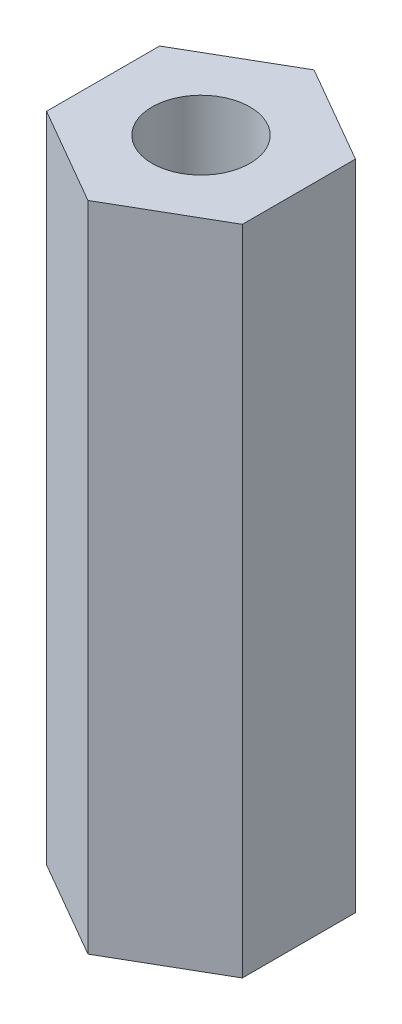
SolidWorks part; units mm, degrees
material "1060 Alloy"
ref_plane "Front Plane" through (0, 0, 0) normal (0, 0, 1) x (1, 0, 0)
ref_plane "Top Plane" through (0, 0, 0) normal (0, 1, 0) x (1, 0, 0)
ref_plane "Right Plane" through (0, 0, 0) normal (1, 0, 0) x (0, 0, -1)
sketch "Sketch1" plane through (0, 0, 0) normal (0, 1, 0) x (1, 0, 0)
  line L1 (0, -3.4641) -> (3, -1.7321)
  line L2 (3, -1.7321) -> (3, 1.7321)
  line L3 (3, 1.7321) -> (0, 3.4641)
  line L4 (0, 3.4641) -> (-3, 1.7321)
  line L5 (-3, 1.7321) -> (-3, -1.7321)
  line L6 (-3, -1.7321) -> (0, -3.4641)
  circle A0 centre (0, 0) radius 3 construction
  circle A1 centre (0, 0) radius 1.5
  dimension "D1" = 3
  dimension "D2" = 6
extrude "Boss-Extrude1" add sketch "Sketch1" along normal blind 20
